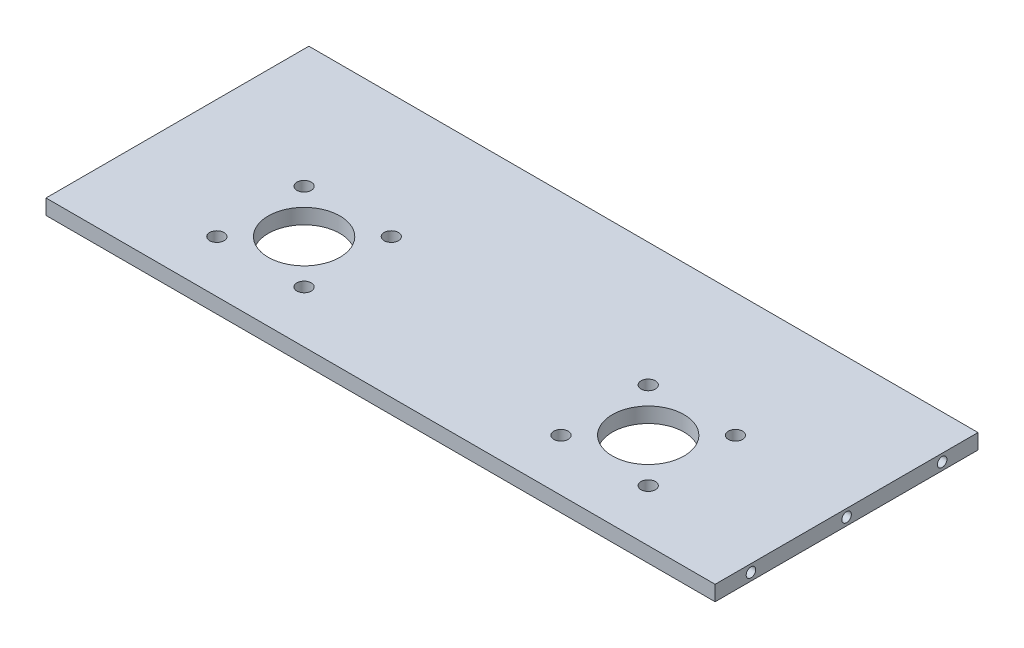
SolidWorks part; units mm, degrees
ref_plane "Alzado" through (0, 0, 0) normal (0, 0, 1) x (1, 0, 0)
ref_plane "Planta" through (0, 0, 0) normal (0, 1, 0) x (1, 0, 0)
ref_plane "Vista lateral" through (0, 0, 0) normal (1, 0, 0) x (0, 0, -1)
sketch "Croquis1" plane through (0, 0, 0) normal (0, 1, 0) x (1, 0, 0)
  line L1 (-125.7057, 56.7568) -> (154.2943, 56.7568)
  line L2 (-125.7057, 56.7568) -> (-125.7057, -53.2432)
  line L3 (-125.7057, -53.2432) -> (154.2943, -53.2432)
  line L4 (154.2943, 56.7568) -> (154.2943, -53.2432)
  dimension "D1" = 280
  dimension "D2" = 110
extrude "Saliente-Extruir1" add sketch "Croquis1" along normal blind 6.35
sketch "Croquis2" plane through (0, 0, 0) normal (0, 1, 0) x (1, 0, 0)
  line L0 (154.2943, -53.2432) -> (154.2943, 56.7568) construction
  line L5 (14.2943, -3.2432) -> (14.2943, 86.0992) construction
  line L6 (14.2943, 86.0992) -> (14.2943, -88.1745) construction
  circle A0 centre (-39.4557, 5.0068) radius 3
  circle A1 centre (-75.9557, 5.0068) radius 3
  circle A2 centre (86.2943, -13.2432) radius 15
  circle A3 centre (-57.7057, -13.2432) radius 15
  circle A4 centre (-39.4557, -31.4932) radius 3
  circle A5 centre (-75.9557, -31.4932) radius 3
  circle A6 centre (104.5443, 5.0068) radius 3
  circle A7 centre (68.0443, 5.0068) radius 3
  circle A8 centre (104.5443, -31.4932) radius 3
  circle A9 centre (68.0443, -31.4932) radius 3
  dimension "D4" = 6
  dimension "D5" = 30
  dimension "D6" = 30
  dimension "D9" = 6
  dimension "D1" = 36.5
  dimension "D2" = 140
  dimension "D3" = 36.5
  dimension "D7" = 72
  dimension "D8" = 72
  dimension "D10" = 36.5
  dimension "D11" = 53.75
  dimension "D12" = 36.5
  dimension "D13" = 53.75
extrude "Cortar-Extruir2" cut sketch "Croquis2" along normal blind 20
sketch "Croquis5" plane through (-125.7057, 0, 0) normal (-1, 0, 0) x (0, 0, 1)
  line L0 (53.2432, 6.35) -> (53.2432, 0) construction
  line L2 (-56.7568, 6.35) -> (-56.7568, 0) construction
  line L4 (-56.7568, 3.175) -> (53.2432, 3.175) construction
  circle A0 centre (38.2432, 3.175) radius 2
  circle A1 centre (-41.7568, 3.175) radius 2
  circle A2 centre (-1.7568, 3.175) radius 2
  dimension "D3" = 4
  dimension "D6" = 4
  dimension "D2" = 4
  dimension "D1" = 15
  dimension "D4" = 15
  dimension "D5" = 40
  dimension "D7" = 40
extrude "Cortar-Extruir5" cut sketch "Croquis5" against normal blind 30
sketch "Croquis6" plane through (154.2943, 0, 0) normal (1, 0, 0) x (0, 0, -1)
  line L1 (-53.2432, 6.35) -> (-53.2432, 0) construction
  line L2 (56.7568, 6.35) -> (56.7568, 0) construction
  line L3 (-53.2432, 3.175) -> (56.7568, 3.175) construction
  circle A0 centre (41.7568, 3.175) radius 2
  circle A1 centre (-38.2432, 3.175) radius 2
  circle A2 centre (1.7568, 3.175) radius 2
  dimension "D1" = 4
  dimension "D2" = 4
  dimension "D3" = 4
  dimension "D4" = 40
  dimension "D5" = 15
  dimension "D6" = 15
  dimension "D7" = 40
extrude "Cortar-Extruir6" cut sketch "Croquis6" against normal blind 30
